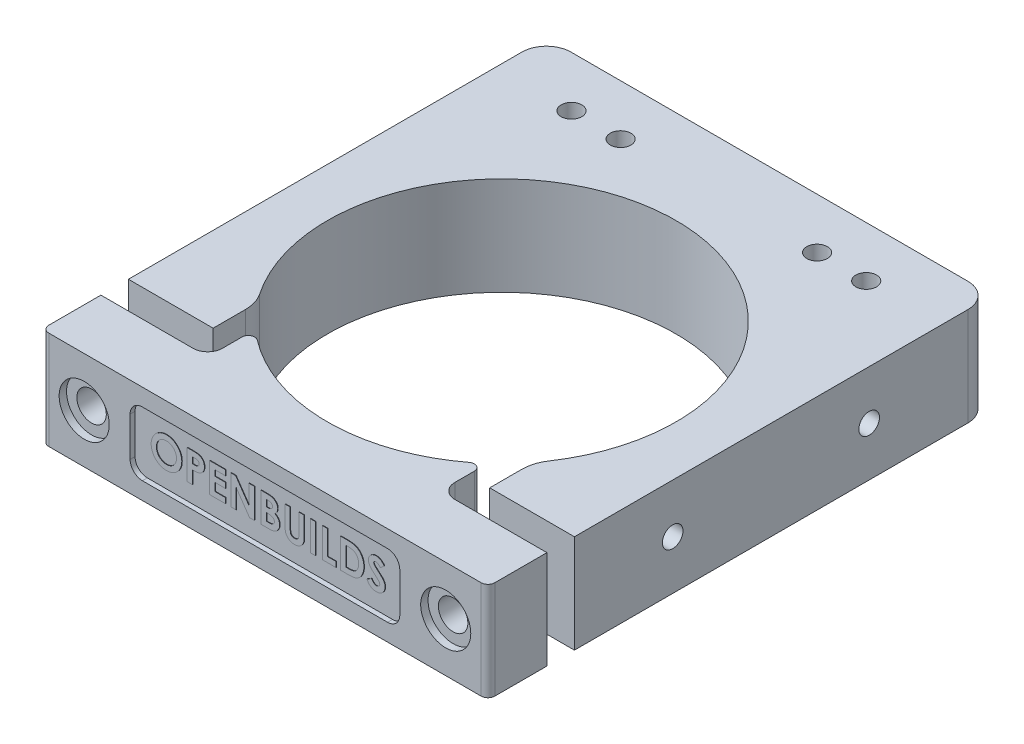
SolidWorks part; units mm, degrees
material "6061-T6 (SS)"
ref_plane "Front Plane" through (0, 0, 0) normal (0, 0, 1) x (1, 0, 0)
ref_plane "Top Plane" through (0, 0, 0) normal (0, 1, 0) x (1, 0, 0)
ref_plane "Right Plane" through (0, 0, 0) normal (1, 0, 0) x (0, 0, -1)
sketch "Sketch1" plane through (0, 0, 0) normal (0, 1, 0) x (1, 0, 0)
  line L0 (-45.4, -30.6) -> (-28.15, -30.6)
  line L1 (-28.15, -30.6) -> (-28.15, -24.0432)
  line L2 (-45.4, -30.6) -> (-45.4, 49.5)
  line L3 (-40.4, 54.5) -> (40.4, 54.5)
  line L4 (0, 54.5) -> (0, 0) construction
  line L5 (45.4, -30.6) -> (45.4, 49.5)
  line L6 (28.15, -30.6) -> (28.15, -24.0432)
  line L7 (45.4, -30.6) -> (28.15, -30.6)
  line L8 (-23.65, -29.2356) -> (-23.65, -33.2)
  line L9 (-26.65, -36.2) -> (-45.4, -36.2)
  line L10 (-45.4, -36.2) -> (-45.4, -46.8)
  line L11 (-44, -48.2) -> (44, -48.2)
  line L12 (0, -48.2) -> (0, -35.5) construction
  line L13 (23.65, -29.2356) -> (23.65, -33.2)
  line L14 (26.65, -36.2) -> (45.4, -36.2)
  line L15 (45.4, -36.2) -> (45.4, -46.8)
  arc A0 (29.432, -19.8497) -> (-29.432, -19.8497) centre (0, 0) ccw
  arc A1 (21.5605, -28.2028) -> (-21.5605, -28.2028) centre (0, 0) cw
  arc A2 (45.4, 49.5) -> (40.4, 54.5) centre (40.4, 49.5) ccw
  arc A3 (-45.4, 49.5) -> (-40.4, 54.5) centre (-40.4, 49.5) cw
  arc A4 (23.65, -33.2) -> (26.65, -36.2) centre (26.65, -33.2) ccw
  arc A5 (-23.65, -33.2) -> (-26.65, -36.2) centre (-26.65, -33.2) cw
  arc A6 (23.65, -29.2356) -> (21.5605, -28.2028) centre (22.35, -29.2356) ccw
  arc A7 (-23.65, -29.2356) -> (-21.5605, -28.2028) centre (-22.35, -29.2356) cw
  arc A8 (28.15, -24.0432) -> (29.432, -19.8497) centre (35.65, -24.0432) cw
  arc A9 (-28.15, -24.0432) -> (-29.432, -19.8497) centre (-35.65, -24.0432) ccw
  arc A10 (-45.4, -46.8) -> (-44, -48.2) centre (-44, -46.8) ccw
  arc A11 (45.4, -46.8) -> (44, -48.2) centre (44, -46.8) cw
  point P23 (45.4, 54.5)
  point P26 (-45.4, 54.5)
  point P29 (23.65, -36.2)
  point P32 (-23.65, -36.2)
  point P35 (23.65, -26.475)
  point P38 (-23.65, -26.475)
  point P41 (28.15, -21.6293)
  point P44 (-28.15, -21.6293)
  point P47 (-45.4, -48.2)
  point P50 (45.4, -48.2)
  dimension "D1" = 71
  dimension "D9" = 5
  dimension "D10" = 3
  dimension "D11" = 1.3
  dimension "D12" = 7.5
  dimension "D13" = 1.4
  dimension "D2" = 90.8
  dimension "D3" = 85.1
  dimension "D4" = 54.5
  dimension "D5" = 17.25
  dimension "D6" = 47.3
  dimension "D7" = 12
  dimension "D8" = 12.7
extrude "Boss-Extrude1" add sketch "Sketch1" along normal blind 20
hole_wizard "M5x0.8 Tapped Hole1" positions "Sketch3" profile "Sketch2" tap size "M5x0.8" standard "ANSI Metric" end condition through all
sketch "Sketch3" plane through (0, 20, 0) normal (0, 1, 0) x (1, 0, 0)
  line L0 (0, 54.5) -> (0, 64.1455) construction
  line L1 (40.4, 54.5) -> (-40.4, 54.5) construction
  point P0 (-30, 44.2)
  point P2 (-20, 44.2)
  point P12 (20, 44.2)
  point P13 (30, 44.2)
  dimension "D1" = 10
  dimension "D2" = 10.3
  dimension "D3" = 60
sketch "Sketch2" plane through (-30, 20, -44.2) normal (1, 0, 0) x (0, 0, 1)
  line L0 (0, 0) -> (0, 20)
  line L1 (0, 20) -> (2.1, 20)
  line L2 (2.1, 20) -> (2.1, 0)
  line L5 (2.1, 0) -> (0, 0)
  line L11 (0, -6.35) -> (0, 107.95) construction
  dimension "Thread Major Dia." = 4.2
  dimension "Thru Tap Drill Depth" = 20
hole_wizard "Hole1" positions "Sketch5" profile "Sketch4" legacy end condition up to next
sketch "Sketch5" plane through (0, 0, 48.2) normal (0, 0, 1) x (1, 0, 0)
  line L0 (45.4, 10) -> (0, 10) construction
  line L1 (45.4, 20) -> (45.4, 0) construction
  line L2 (0, 10) -> (0, 20) construction
  line L3 (-44, 20) -> (44, 20) construction
  point P0 (36.8, 10)
  point P14 (-36.8, 10)
  dimension "D1" = 73.6
sketch "Sketch4" plane through (36.8, 10, 48.2) normal (1, 0, 0) x (0, -1, 0)
  line L0 (0, 0) -> (0, 12)
  line L1 (0, 12) -> (3, 12)
  line L2 (3, 12) -> (3, 1.5)
  line L3 (3, 1.5) -> (5.1, 1.5)
  line L4 (5.1, 1.5) -> (5.1, 0)
  line L5 (5.1, 0) -> (0, 0)
  line L6 (0, 110) -> (0, -10) construction
  dimension "Diameter" = 6
  dimension "Depth" = 12
  dimension "C-Bore Diameter" = 10.2
  dimension "C-Bore Depth" = 1.5
hole_wizard "M5x0.8 Tapped Hole2" positions "Sketch7" profile "Sketch6" tap size "M5x0.8" standard "ANSI Metric"
sketch "Sketch7" plane through (0, 0, 30.6) normal (0, 0, 1) x (1, 0, 0)
  point P0 (36.8, 10)
  point P3 (-36.8, 10)
sketch "Sketch6" plane through (36.8, 10, 30.6) normal (1, 0, 0) x (0, -1, 0)
  line L0 (0, 0) -> (0, 14.2618)
  line L1 (0, 14.2618) -> (2.1, 13)
  line L2 (2.1, 13) -> (2.1, 0)
  line L5 (2.1, 0) -> (0, 0)
  line L10 (0, 14.2618) -> (-2.1, 13) construction
  line L11 (0, -6.35) -> (0, 107.95) construction
  dimension "Tap Drill Dia." = 4.2
  dimension "Tap Drill Depth" = 13
  dimension "Drill Angle" = 118
hole_wizard "M5x0.8 Tapped Hole3" positions "Sketch9" profile "Sketch8" tap size "M5x0.8" standard "ANSI Metric"
sketch "Sketch9" plane through (45.4, 0, 0) normal (1, 0, 0) x (0, 0, -1)
  line L0 (-30.6, 10) -> (9.4, 10) construction
  line L2 (9.4, 10) -> (9.4, 28.1891) construction
  line L5 (-30.6, 20) -> (-30.6, 0) construction
  point P14 (-10.6, 10)
  point P17 (29.4, 10)
  dimension "D1" = 20
  dimension "D2" = 40
sketch "Sketch8" plane through (45.4, 10, 10.6) normal (0, 1, 0) x (0, 0, -1)
  line L0 (0, 0) -> (0, 10.2618)
  line L1 (0, 10.2618) -> (2.1, 9)
  line L2 (2.1, 9) -> (2.1, 0)
  line L5 (2.1, 0) -> (0, 0)
  line L10 (0, 10.2618) -> (-2.1, 9) construction
  line L11 (0, -6.35) -> (0, 107.95) construction
  dimension "Tap Drill Dia." = 4.2
  dimension "Tap Drill Depth" = 9
  dimension "Drill Angle" = 118
mirror "Mirror1" about plane through (0, 0, 0) normal (1, 0, 0) of "M5x0.8 Tapped Hole3"
hole_wizard "M5x0.8 Tapped Hole4" positions "Sketch11" profile "Sketch10" tap size "M5x0.8" standard "ANSI Metric"
sketch "Sketch11" plane through (0, 0, -54.5) normal (0, 0, -1) x (-1, 0, 0)
  line L0 (-45.4, 10) -> (0, 10) construction
  line L1 (-45.4, 20) -> (-45.4, 0) construction
  line L2 (0, 10) -> (0, 0) construction
  point P10 (-30, 10)
  point P12 (-10, 10)
  point P15 (30, 10)
  point P16 (10, 10)
  dimension "D1" = 60
  dimension "D2" = 20
sketch "Sketch10" plane through (30, 10, -54.5) normal (1, 0, 0) x (0, 1, 0)
  line L0 (0, 0) -> (0, 8.2618)
  line L1 (0, 8.2618) -> (2.1, 7)
  line L2 (2.1, 7) -> (2.1, 0)
  line L5 (2.1, 0) -> (0, 0)
  line L10 (0, 8.2618) -> (-2.1, 7) construction
  line L11 (0, -6.35) -> (0, 107.95) construction
  dimension "Tap Drill Dia." = 4.2
  dimension "Tap Drill Depth" = 7
  dimension "Drill Angle" = 118
sketch "Sketch12" plane through (0, 0, 48.2) normal (0, 0, 1) x (1, 0, 0)
  line L0 (-27.45, 10) -> (-45.4, 10) construction
  line L1 (-24.95, 16.5) -> (24.95, 16.5)
  line L2 (-27.45, 14) -> (-27.45, 6)
  line L3 (-24.95, 3.5) -> (24.95, 3.5)
  line L4 (27.45, 14) -> (27.45, 6)
  line L5 (-45.4, 20) -> (-45.4, 0) construction
  line L6 (0, 3.5) -> (0, 0) construction
  arc A0 (-27.45, 6) -> (-24.95, 3.5) centre (-24.95, 6) ccw
  arc A1 (24.95, 3.5) -> (27.45, 6) centre (24.95, 6) ccw
  arc A2 (24.95, 16.5) -> (27.45, 14) centre (24.95, 14) cw
  arc A3 (-24.95, 16.5) -> (-27.45, 14) centre (-24.95, 14) ccw
  point P13 (-27.45, 3.5)
  point P18 (27.45, 16.5)
  point P21 (-27.45, 16.5)
  dimension "D3" = 2.5
  dimension "D1" = 13
  dimension "D2" = 54.9
extrude "Cut-Extrude1" cut sketch "Sketch12" against normal blind 1
sketch "Sketch13" plane through (0, 0, 47.2) normal (0, 0, 1) x (1, 0, 0)
  line L0 (-24.95, 3.5) -> (24.95, 3.5) construction
  line L1 (-27.45, 14) -> (-27.45, 6) construction
  text T0 "<b>OPENBUILDS</b>" font "Century Gothic" height 6
  dimension "D1" = 3.5
  dimension "D2" = 3
extrude "Boss-Extrude2" add sketch "Sketch13" along normal blind 0.1
